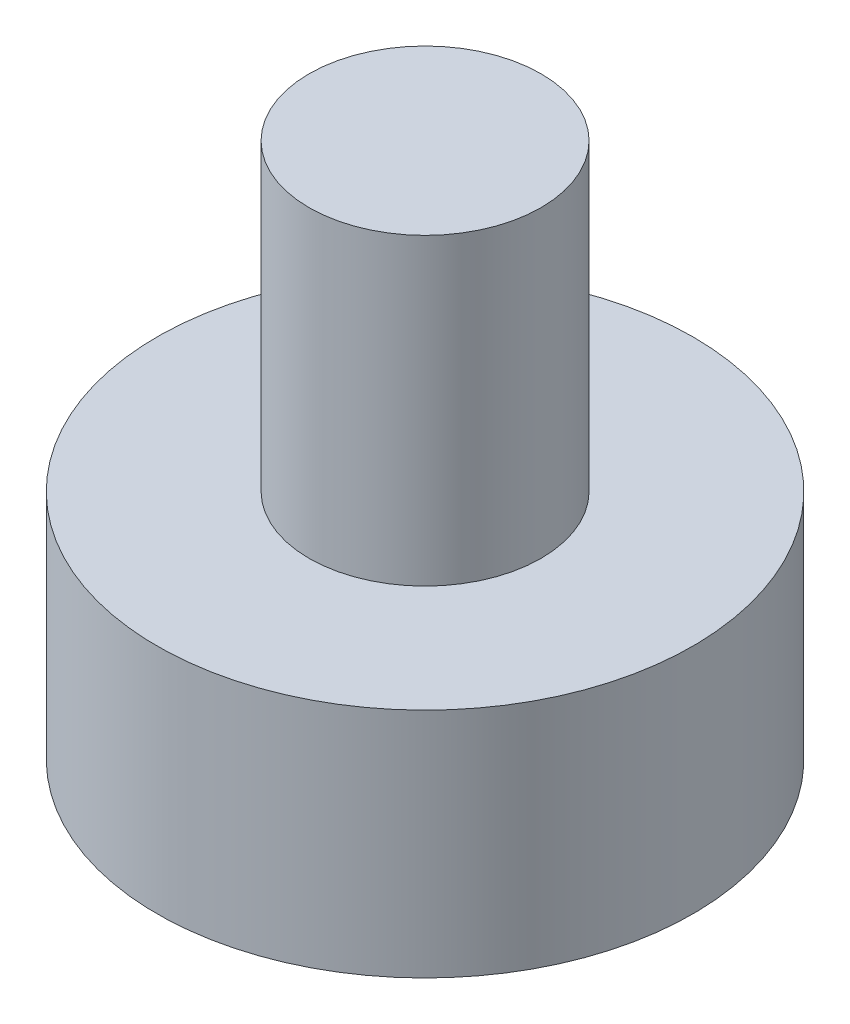
SolidWorks part; units mm, degrees
ref_plane "Front Plane" through (0, 0, 0) normal (0, 0, 1) x (1, 0, 0)
ref_plane "Top Plane" through (0, 0, 0) normal (0, 1, 0) x (1, 0, 0)
ref_plane "Right Plane" through (0, 0, 0) normal (1, 0, 0) x (0, 0, -1)
sketch "Sketch1" plane through (0, 0, 0) normal (0, 1, 0) x (1, 0, 0)
  circle A0 centre (0, 0) radius 21
  dimension "D1" = 42
extrude "Boss-Extrude1" add sketch "Sketch1" along normal blind 55
sketch "Sketch2" plane through (0, 0, 0) normal (0, -1, 0) x (1, 0, 0)
  circle A0 centre (0, 0) radius 48.5
  dimension "D1" = 97
extrude "Boss-Extrude2" add sketch "Sketch2" along normal blind 42
